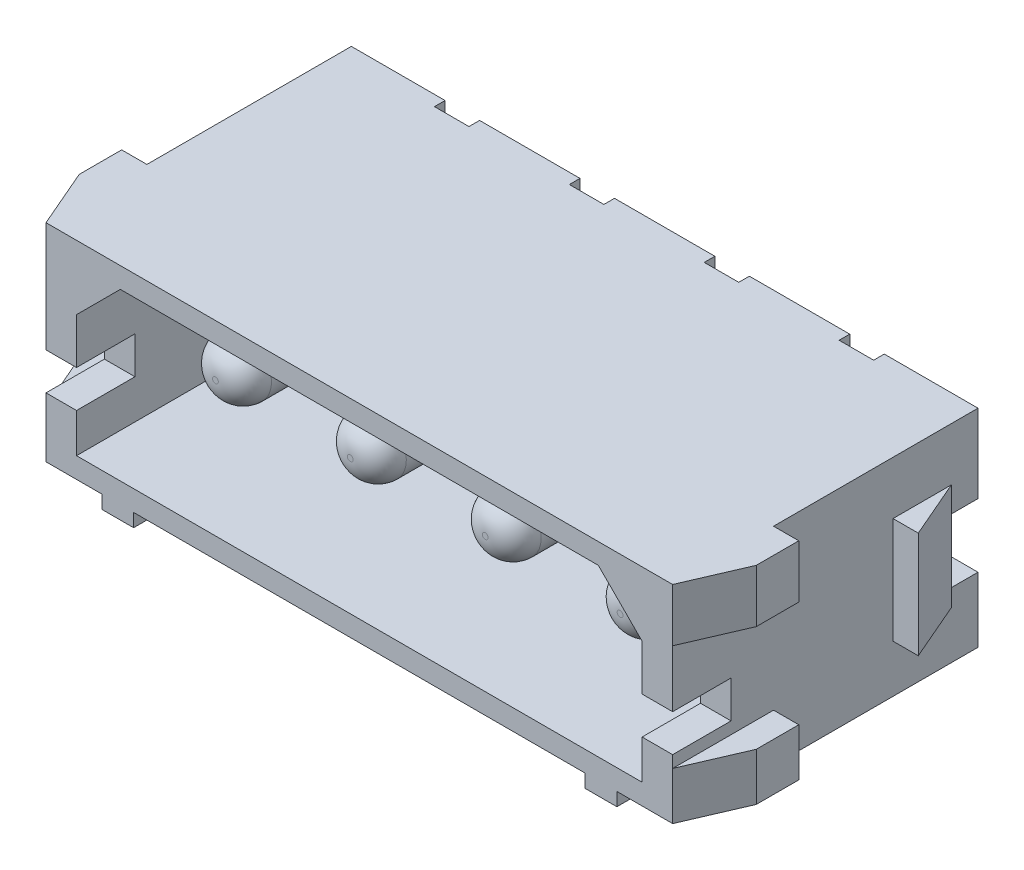
SolidWorks part; units mm, degrees
ref_plane "Front Plane" through (0, 0, 0) normal (0, 0, 1) x (1, 0, 0)
ref_plane "Top Plane" through (0, 0, 0) normal (0, 1, 0) x (1, 0, 0)
ref_plane "Right Plane" through (0, 0, 0) normal (1, 0, 0) x (0, 0, -1)
sketch "Sketch1" plane through (0, 0, 0) normal (0, 1, 0) x (1, 0, 0)
  line L0 (-11.8, 0) -> (11.8, 0)
  line L1 (11.8, 0) -> (11.8, -1)
  line L2 (11.8, -1) -> (12.75, -3.2)
  line L3 (12.75, -3.2) -> (11.8, -3.2)
  line L4 (11.8, -3.2) -> (11.8, -7.7)
  line L5 (11.8, -7.7) -> (12.75, -7.7)
  line L6 (12.75, -7.7) -> (12.75, -9.3)
  line L7 (11.8, -11.5) -> (-11.8, -11.5)
  line L8 (-12.75, -7.7) -> (-12.75, -9.3)
  line L9 (-12.75, -7.7) -> (-11.8, -7.7)
  line L10 (-11.8, -7.7) -> (-11.8, -3.2)
  line L11 (-11.8, -3.2) -> (-12.75, -3.2)
  line L12 (-12.75, -3.2) -> (-11.8, -1)
  line L13 (-11.8, -1) -> (-11.8, 0)
  line L14 (12.75, -9.3) -> (11.8, -11.5)
  line L15 (-12.75, -9.3) -> (-11.8, -11.5)
  line L16 (11.8, -5.45) -> (14.4714, -5.45) construction
  dimension "D1" = 11.5
  dimension "D2" = 23.6
  dimension "D3" = 0.95
  dimension "D4" = 5.45
  dimension "D5" = 1
  dimension "D6" = 4.5
  dimension "D7" = 1.6
extrude "Boss-Extrude1" add sketch "Sketch1" along normal mid plane 8.3
sketch "Sketch2" plane through (0, 0, 11.5) normal (0, 0, 1) x (1, 0, 0)
  line L0 (0, 0) -> (0, -12.0536) construction
  line L1 (19.7, -8.65) -> (9.7, -8.65)
  line L2 (19.7, -8.65) -> (19.7, -3.65)
  line L3 (19.7, -3.65) -> (9.7, -3.65)
  line L4 (9.7, -8.65) -> (9.7, -3.65)
  line L5 (-9.7, -8.65) -> (-19.7, -8.65)
  line L6 (-9.7, -8.65) -> (-9.7, -3.65)
  line L7 (-9.7, -3.65) -> (-19.7, -3.65)
  line L8 (-19.7, -8.65) -> (-19.7, -3.65)
  line L9 (-8.5, -8.65) -> (8.5, -8.65)
  line L10 (-8.5, -8.65) -> (-8.5, -3.65)
  line L11 (-8.5, -3.65) -> (8.5, -3.65)
  line L12 (8.5, -8.65) -> (8.5, -3.65)
  line L13 (-11.8, -4.15) -> (11.8, -4.15) construction
  dimension "D1" = 1.2
  dimension "D2" = 17
  dimension "D3" = 10
  dimension "D4" = 0.5
  dimension "D5" = 5
extrude "Cut-Extrude1" cut sketch "Sketch2" against normal through all
sketch "Sketch3" plane through (0, 0, 11.5) normal (0, 0, 1) x (1, 0, 0)
  line L0 (-11.8, 4.15) -> (11.8, 4.15) construction
  line L1 (16.8, 2.15) -> (11.8, 2.15)
  line L2 (16.8, 2.15) -> (16.8, -1.85)
  line L3 (16.8, -1.85) -> (11.8, -1.85)
  line L4 (11.8, 2.15) -> (11.8, -1.85)
  line L5 (-16.8, 2.15) -> (-11.8, 2.15)
  line L6 (-16.8, 2.15) -> (-16.8, -1.85)
  line L7 (-16.8, -1.85) -> (-11.8, -1.85)
  line L8 (-11.8, 2.15) -> (-11.8, -1.85)
  line L9 (-11.8, 4.15) -> (-11.8, -3.65) construction
  line L10 (11.8, 4.15) -> (11.8, -3.65) construction
  dimension "D1" = 4
  dimension "D2" = 2
  dimension "D3" = 5
  dimension "D4" = 5
extrude "Cut-Extrude2" cut sketch "Sketch3" against normal blind 6.3
sketch "Sketch4" plane through (0, 0, 0) normal (0, 0, -1) x (-1, 0, 0)
  line L0 (11.8, 4.15) -> (11.8, -3.65) construction
  line L1 (11.8, 6.6904) -> (16.8, 6.6904)
  line L2 (11.8, 6.6904) -> (11.8, 2.15)
  line L3 (11.8, 2.15) -> (16.8, 2.15)
  line L4 (16.8, 6.6904) -> (16.8, 2.15)
  line L5 (16.8, -1.85) -> (11.8, -1.85)
  line L6 (16.8, -1.85) -> (16.8, -6.85)
  line L7 (16.8, -6.85) -> (11.8, -6.85)
  line L8 (11.8, -1.85) -> (11.8, -6.85)
  line L9 (-11.8, -6.85) -> (-16.8, -6.85)
  line L10 (-11.8, -6.85) -> (-11.8, -1.85)
  line L11 (-11.8, -1.85) -> (-16.8, -1.85)
  line L12 (-16.8, -6.85) -> (-16.8, -1.85)
  line L13 (-11.8, 7.15) -> (-16.8, 7.15)
  line L14 (-11.8, 7.15) -> (-11.8, 2.15)
  line L15 (-11.8, 2.15) -> (-16.8, 2.15)
  line L16 (-16.8, 7.15) -> (-16.8, 2.15)
  line L17 (-11.8, 4.15) -> (-11.8, -3.65) construction
  line L18 (-11.8, 4.15) -> (11.8, 4.15) construction
  dimension "D1" = 4
  dimension "D2" = 2
  dimension "D3" = 5
  dimension "D4" = 5
  dimension "D5" = 5
extrude "Cut-Extrude3" cut sketch "Sketch4" against normal blind 6.3
sketch "Sketch5" plane through (0, 0, 11.5) normal (0, 0, 1) x (1, 0, 0)
  line L0 (-10.65, -2.875) -> (10.65, -2.875)
  line L1 (10.65, -2.875) -> (10.65, 1.725)
  line L2 (10.65, 1.725) -> (9, 3.375)
  line L3 (9, 3.375) -> (-9, 3.375)
  line L4 (-9, 3.375) -> (-10.65, 1.725)
  line L5 (-10.65, 1.725) -> (-10.65, -2.875)
  line L6 (0, 0) -> (0, 3.375) construction
  line L7 (0, 0) -> (0, -2.875) construction
  line L8 (-11.8, 4.15) -> (11.8, 4.15) construction
  dimension "D1" = 21.3
  dimension "D2" = 6.25
  dimension "D3" = 0.775
  dimension "D4" = 18
  dimension "D5" = 45
extrude "Cut-Extrude4" cut sketch "Sketch5" against normal blind 7.3
sketch "Sketch6" plane through (0, 0, 4.2) normal (0, 0, 1) x (1, 0, 0)
  line L0 (-7.62, 0) -> (7.62, 0) construction
  circle A0 centre (-7.62, 0) radius 1.11
  circle A1 centre (-2.54, 0) radius 1.11
  circle A2 centre (2.54, 0) radius 1.11
  circle A3 centre (7.62, 0) radius 1.11
  dimension "D3" = 5.08
  dimension "D4" = 2.54
  dimension "D5" = 2.22
  dimension "D1" = 5.08
  dimension "D2" = 5.08
extrude "Boss-Extrude2" add sketch "Sketch6" along normal blind 5.1
fillet "Fillet1" radius 1 4 edges at (8.73, 0, 9.3) (3.65, 0, 9.3) (-1.43, 0, 9.3) (-6.51, 0, 9.3)
sketch "Sketch7" plane through (11.8, 0, 0) normal (1, 0, 0) x (0, 0, -1)
  line L0 (0, 0) -> (-9.3, 0) construction
  line L1 (-14.3, 0) -> (-9.3, 0)
  line L2 (-14.3, 0) -> (-14.3, -1.4)
  line L3 (-14.3, -1.4) -> (-9.3, -1.4)
  line L4 (-9.3, 0) -> (-9.3, -1.4)
  line L5 (-11.5, 2.15) -> (-11.5, -1.85) construction
  dimension "D1" = 1.4
  dimension "D2" = 2.2
  dimension "D3" = 5
extrude "Cut-Extrude5" cut sketch "Sketch7" against normal through all
sketch "Sketch8" plane through (0, 4.15, 0) normal (0, 1, 0) x (1, 0, 0)
  line L0 (-7.62, -0.4) -> (-7.62, -3.1814) construction
  line L1 (-8.27, 2.6) -> (-6.97, 2.6)
  line L2 (-8.27, 2.6) -> (-8.27, -0.4)
  line L3 (-8.27, -0.4) -> (-6.97, -0.4)
  line L4 (-6.97, 2.6) -> (-6.97, -0.4)
  line L5 (-3.19, 2.6) -> (-1.89, 2.6)
  line L6 (-3.19, 2.6) -> (-3.19, -0.4)
  line L7 (-3.19, -0.4) -> (-1.89, -0.4)
  line L8 (-1.89, 2.6) -> (-1.89, -0.4)
  line L9 (1.89, 2.6) -> (3.19, 2.6)
  line L10 (1.89, 2.6) -> (1.89, -0.4)
  line L11 (1.89, -0.4) -> (3.19, -0.4)
  line L12 (3.19, 2.6) -> (3.19, -0.4)
  line L13 (6.97, 2.6) -> (8.27, 2.6)
  line L14 (6.97, 2.6) -> (6.97, -0.4)
  line L15 (6.97, -0.4) -> (8.27, -0.4)
  line L16 (8.27, 2.6) -> (8.27, -0.4)
  line L17 (-2.54, -0.4) -> (-2.54, -2.4701) construction
  line L18 (2.54, -0.4) -> (2.54, -1.7983) construction
  line L19 (7.62, -0.4) -> (7.62, -1.7983) construction
  line L20 (11.8, 0) -> (-11.8, 0) construction
  dimension "D1" = 5.08
  dimension "D2" = 5.08
  dimension "D3" = 5.08
  dimension "D4" = 2.54
  dimension "D5" = 0.4
  dimension "D6" = 3
  dimension "D7" = 1.3
extrude "Cut-Extrude6" cut sketch "Sketch8" against normal through all
sketch "Sketch9" plane through (11.8, 0, 0) normal (1, 0, 0) x (0, 0, -1)
  line L0 (-1, 2.15) -> (-1, -1.85) construction
  line L1 (2, 1.2) -> (-1, 1.2)
  line L2 (2, 1.2) -> (2, -1.2)
  line L3 (2, -1.2) -> (-1, -1.2)
  line L4 (-1, 1.2) -> (-1, -1.2)
  line L5 (0, 0) -> (2, 0) construction
  dimension "D1" = 2.4
  dimension "D2" = 3
extrude "Cut-Extrude7" cut sketch "Sketch9" against normal through all
sketch "Sketch10" plane through (0, -1.2, 0) normal (0, 1, 0) x (1, 0, 0)
  line L1 (-8.27, -0.4) -> (-6.97, -0.4)
  line L2 (-8.27, -0.4) -> (-8.27, 0)
  line L3 (-8.27, 0) -> (-6.97, 0)
  line L4 (-6.97, -0.4) -> (-6.97, 0)
  line L5 (-3.19, -0.4) -> (-1.89, -0.4)
  line L6 (-3.19, -0.4) -> (-3.19, 0)
  line L7 (-3.19, 0) -> (-1.89, 0)
  line L8 (-1.89, -0.4) -> (-1.89, 0)
  line L9 (1.89, -0.4) -> (3.19, -0.4)
  line L10 (1.89, -0.4) -> (1.89, 0)
  line L11 (1.89, 0) -> (3.19, 0)
  line L12 (3.19, -0.4) -> (3.19, 0)
  line L13 (6.97, -0.4) -> (8.27, -0.4)
  line L14 (6.97, -0.4) -> (6.97, 0)
  line L15 (6.97, 0) -> (8.27, 0)
  line L16 (8.27, -0.4) -> (8.27, 0)
extrude "Boss-Extrude3" add sketch "Sketch10" against normal blind 6.5
sketch "Sketch11" plane through (0, 0, 0) normal (0, 0, -1) x (-1, 0, 0)
  line L1 (-10, -4.95) -> (10, -4.95)
  line L2 (-10, -4.95) -> (-10, -9.95)
  line L3 (-10, -9.95) -> (10, -9.95)
  line L4 (10, -4.95) -> (10, -9.95)
  line L5 (0, 0) -> (0, -4.95) construction
  line L6 (8.5, -4.15) -> (9.7, -4.15) construction
  dimension "D1" = 20
  dimension "D2" = 0.8
  dimension "D3" = 5
extrude "Cut-Extrude8" cut sketch "Sketch11" against normal through all
